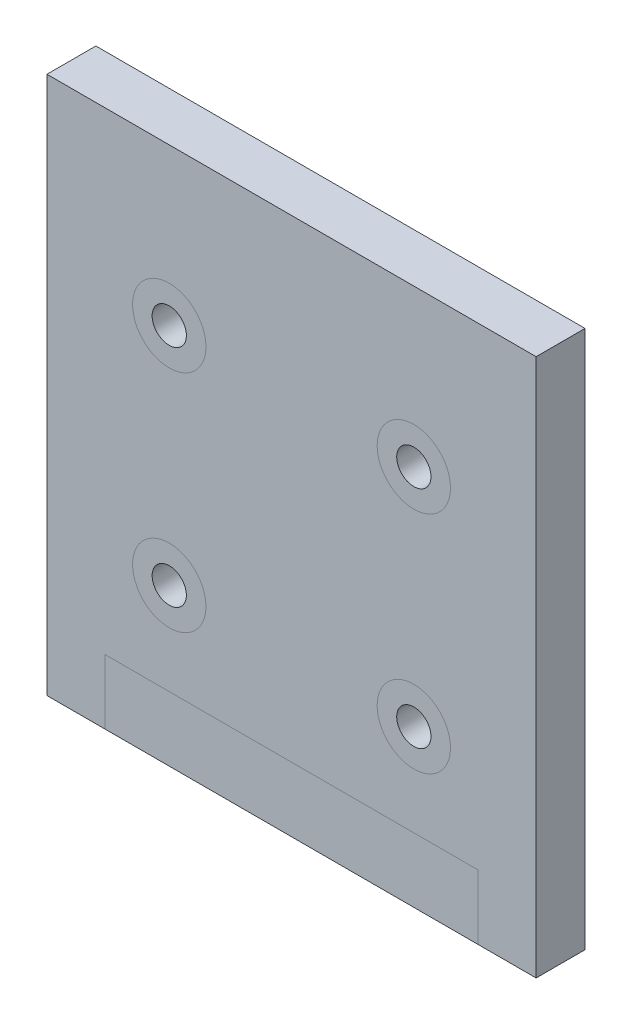
SolidWorks part; units mm, degrees
ref_plane "Front Plane" through (0, 0, 0) normal (0, 0, 1) x (1, 0, 0)
ref_plane "Top Plane" through (0, 0, 0) normal (0, 1, 0) x (1, 0, 0)
ref_plane "Right Plane" through (0, 0, 0) normal (1, 0, 0) x (0, 0, -1)
other "Configuration Table"
sketch "Sketch1" plane through (0, 0, 0) normal (0, 0, 1) x (1, 0, 0)
  line L1 (0, 0) -> (127, 0)
  line L2 (0, 0) -> (0, 139.7)
  line L3 (0, 139.7) -> (127, 139.7)
  line L4 (127, 0) -> (127, 139.7)
  circle A0 centre (31.75, 40.64) radius 4.445
  circle A1 centre (95.25, 40.64) radius 4.445
  circle A2 centre (31.75, 99.06) radius 4.445
  circle A3 centre (95.25, 99.06) radius 4.445
  dimension "D3" = 8.89
  dimension "D1" = 127
  dimension "D2" = 139.7
  dimension "D4" = 40.64
  dimension "D5" = 31.75
extrude "Extrude1" add sketch "Sketch1" along normal blind 12.7
sketch "Sketch2" plane through (0, 0, 12.7) normal (0, 0, 1) x (1, 0, 0)
  line L0 (0, 0) -> (127, 0) construction
  line L1 (15.113, -18.5901) -> (111.887, -18.5901)
  line L2 (15.113, -18.5901) -> (15.113, 16.764)
  line L3 (15.113, 16.764) -> (111.887, 16.764)
  line L4 (111.887, -18.5901) -> (111.887, 16.764)
  line L6 (127, 0) -> (127, 139.7) construction
  dimension "D1" = 16.764
  dimension "D2" = 96.774
  dimension "D3" = 15.113
split line "Split Line1"
sketch "Sketch3" plane through (0, 0, 12.7) normal (0, 0, 1) x (1, 0, 0)
  circle A0 centre (31.75, 99.06) radius 9.525
  circle A1 centre (31.75, 99.06) radius 4.445 construction
  dimension "D1" = 19.05
split line "Split Line2"
sketch "Sketch4" plane through (0, 0, 12.7) normal (0, 0, 1) x (1, 0, 0)
  circle A0 centre (95.25, 99.06) radius 9.525
  circle A1 centre (95.25, 99.06) radius 4.445 construction
  dimension "D1" = 19.05
split line "Split Line3"
sketch "Sketch5" plane through (0, 0, 12.7) normal (0, 0, 1) x (1, 0, 0)
  circle A0 centre (31.75, 40.64) radius 9.525
  circle A1 centre (31.75, 40.64) radius 4.445 construction
  dimension "D1" = 19.05
split line "Split Line4"
sketch "Sketch6" plane through (0, 0, 12.7) normal (0, 0, 1) x (1, 0, 0)
  circle A0 centre (95.25, 40.64) radius 9.525
  circle A1 centre (95.25, 40.64) radius 4.445 construction
  dimension "D1" = 19.05
split line "Split Line5"
